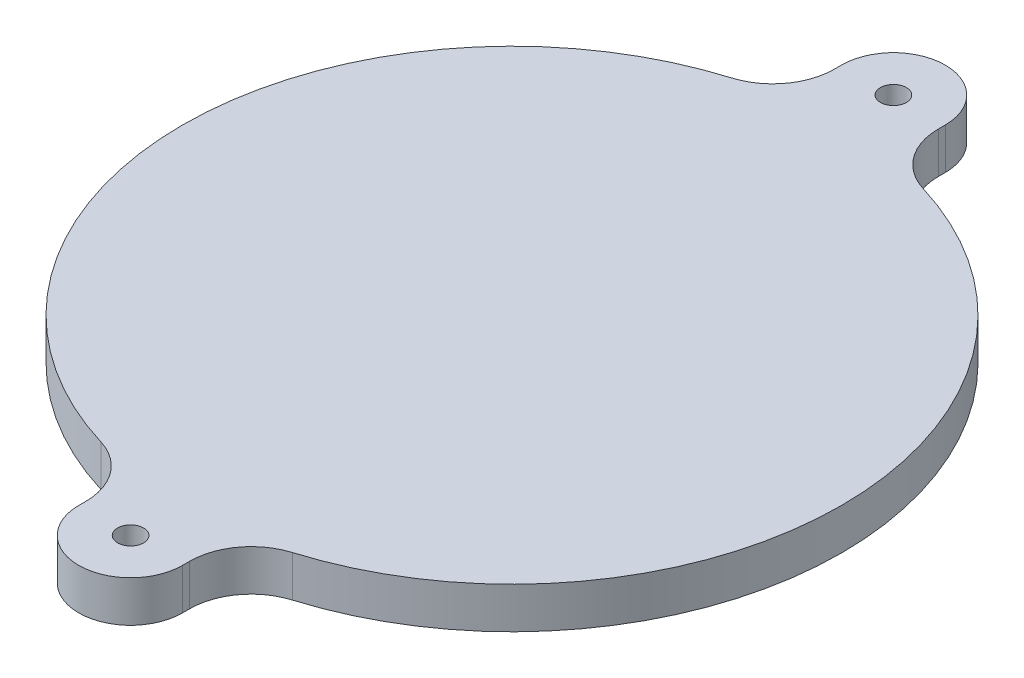
SolidWorks part; units mm, degrees
material "Acrylic (Medium-high impact)"
ref_plane "Front Plane" through (0, 0, 0) normal (0, 0, 1) x (1, 0, 0)
ref_plane "Top Plane" through (0, 0, 0) normal (0, 1, 0) x (1, 0, 0)
ref_plane "Right Plane" through (0, 0, 0) normal (1, 0, 0) x (0, 0, -1)
sketch "Sketch1" plane through (0, -0.3969, 0) normal (0, -1, 0) x (1, 0, 0)
  line L0 (0, 29.4) -> (0, -29.4) construction
  line L1 (4, 29.4) -> (4, -29.4)
  line L2 (-4, 29.4) -> (-4, -29.4)
  circle A0 centre (0, 0) radius 25.4
  circle A1 centre (0, 0) radius 25.4 construction
  arc A2 (4, 29.4) -> (-4, 29.4) centre (0, 29.4) ccw
  arc A3 (-4, -29.4) -> (4, -29.4) centre (0, -29.4) ccw
  circle A4 centre (0, 29.4) radius 1
  circle A5 centre (0, -29.4) radius 1
  point P7 (0, 0)
  dimension "D1" = 2
  dimension "D2" = 8
extrude "Boss-Extrude1" add sketch "Sketch1" along normal blind 3.175 from offset 1
fillet "Fillet1" radius 4.7625 4 edges at (-4, -2.9844, -25.0831) (-4, -2.9844, 25.0831) (4, -2.9844, 25.0831) (4, -2.9844, -25.0831)
sketch "Sketch2" plane through (0, -4.5719, 0) normal (0, -1, 0) x (1, 0, 0)
  line L0 (-19.05, -32.9956) -> (19.05, 32.9956)
  line L1 (-19.05, -32.9956) -> (46.9411, -71.0956)
  line L2 (19.05, 32.9956) -> (85.0411, -5.1044)
  line L3 (46.9411, -71.0956) -> (85.0411, -5.1044)
  line L4 (0, 29.4) -> (0, 0) construction
  point P0 (0, 0)
  dimension "D1" = 30
  dimension "D2" = 76.2
extrude "Cut-Extrude1" [suppressed] cut sketch "Sketch2" against normal through all both and the other way through all
